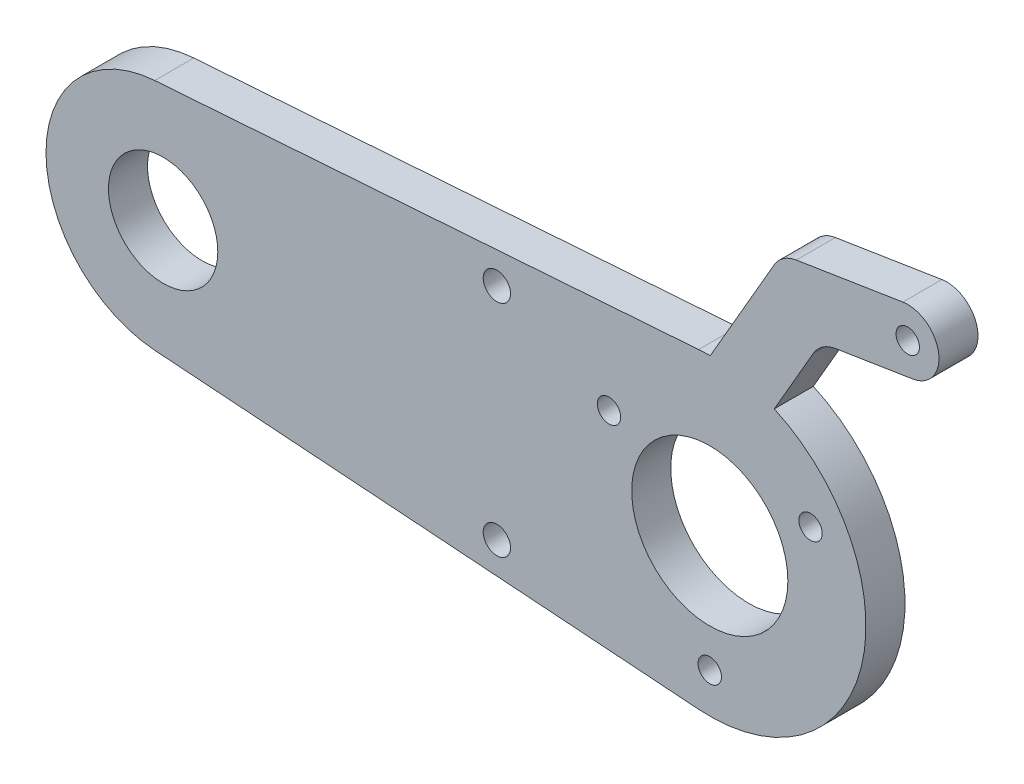
SolidWorks part; units mm, degrees
ref_plane "Front Plane" through (0, 0, 0) normal (0, 0, 1) x (1, 0, 0)
ref_plane "Top Plane" through (0, 0, 0) normal (0, 1, 0) x (1, 0, 0)
ref_plane "Right Plane" through (0, 0, 0) normal (1, 0, 0) x (0, 0, -1)
sketch "Sketch1" plane through (0, 0, 0) normal (0, 0, 1) x (1, 0, 0)
  line L0 (-71.0714, 14.9617) -> (-1.4286, 19.9489)
  line L1 (-71.0714, -14.9617) -> (-1.4286, -19.9489)
  line L2 (8.243, 34.178) -> (0.0573, 19.9999)
  line L3 (11.0813, 36.1287) -> (24.7271, 38.29)
  line L5 (25.9785, 30.3885) -> (16.1016, 28.8241)
  line L6 (13.2633, 26.8734) -> (8.2633, 18.2131)
  line L7 (0, 0) -> (0, 20.1614) construction
  arc A0 (-1.4286, -19.9489) -> (-1.4286, 19.9489) centre (0, 0) ccw construction
  arc A1 (-71.0714, -14.9617) -> (-71.0714, 14.9617) centre (-70, 0) cw
  circle A3 centre (-70, 0) radius 7
  circle A4 centre (0, 0) radius 10
  circle A5 centre (-12.9038, 7.45) radius 1.5
  circle A6 centre (0, -14.9) radius 1.5
  arc A10 (0.0573, 19.9999) -> (-1.4286, 19.9489) centre (0, 0) ccw
  arc A11 (8.2633, 18.2131) -> (-1.4286, -19.9489) centre (0, 0) cw
  arc A12 (25.9785, 30.3885) -> (24.7271, 38.29) centre (25.3528, 34.3392) ccw
  circle A16 centre (-27.2623, 14.0887) radius 1.75
  circle A17 centre (-27.2623, -14.0887) radius 1.75
  circle A18 centre (12.9038, 7.45) radius 1.5
  arc A19 (8.243, 34.178) -> (11.0813, 36.1287) centre (11.7071, 32.178) cw
  arc A20 (16.1016, 28.8241) -> (13.2633, 26.8734) centre (16.7274, 24.8734) ccw
  circle A21 centre (25.3528, 34.3392) radius 1.5
  point P9 (-85, 0)
  dimension "D2" = 20
  dimension "D3" = 15
  dimension "D6" = 3
  dimension "D7" = 14
  dimension "D10" = 3.5
  dimension "D13" = 3.5
  dimension "D5" = 3
  dimension "D4" = 20
  dimension "D9" = 3
  dimension "D16" = 8
  dimension "D17" = 8
  dimension "D18" = 4
  dimension "D19" = 3
  dimension "D1" = 70
  dimension "D8" = 15
  dimension "D11" = 4
  dimension "D12" = 45
  dimension "D14" = 4
  dimension "D15" = 45
  dimension "D20" = 10
  dimension "D21" = 10
  dimension "D22" = 30
  dimension "D23" = 129
extrude "Boss-Extrude1" add sketch "Sketch1" along normal blind 5
move or copy body "Body-Move/Copy1" bodies to move or copy 101
